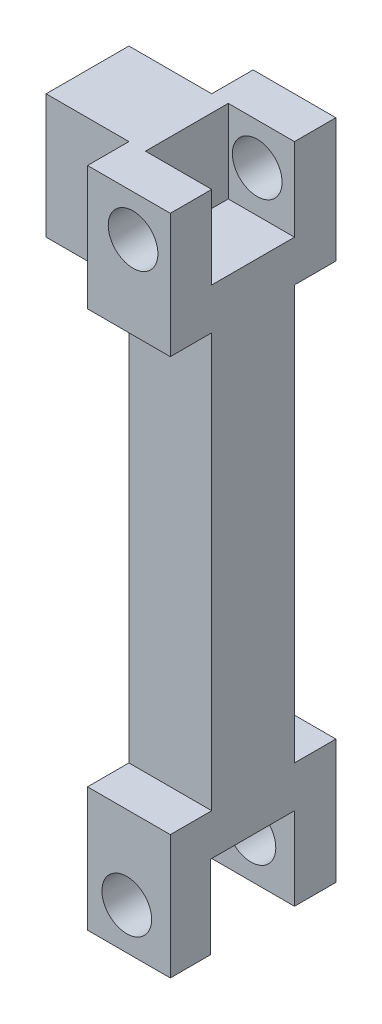
SolidWorks part; units mm, degrees
ref_plane "Front" through (0, 0, 0) normal (0, 0, 1) x (1, 0, 0)
ref_plane "Top" through (0, 0, 0) normal (0, 1, 0) x (1, 0, 0)
ref_plane "Right" through (0, 0, 0) normal (1, 0, 0) x (0, 0, -1)
sketch "Sketch1" plane through (0, 0, 0) normal (0, 0, 1) x (1, 0, 0)
  line L0 (-4.5761, -135.7066) -> (-29.9761, -135.7066)
  line L1 (-29.9761, 67.4934) -> (-4.5761, 67.4934)
  line L2 (-29.9761, 29.3934) -> (-29.9761, -135.7066)
  line L4 (-4.5761, 67.4934) -> (-4.5761, -135.7066)
  line L5 (-29.9761, 67.4934) -> (-55.3761, 67.4934)
  line L7 (-29.9761, 29.3934) -> (-55.3761, 29.3934)
  line L8 (-55.3761, 67.4934) -> (-55.3761, 29.3934)
  dimension "D1" = 25.4
  dimension "D2" = 203.2
  dimension "D3" = 25.4
  dimension "D4" = 38.1
extrude "Base-Extrude" add sketch "Sketch1" against normal blind 25.4
sketch "Sketch7" plane through (-29.9761, 0, 0) normal (-1, 0, 0) x (0, 0, 1)
  line L0 (0, 26.7505) -> (0, -135.7066) construction
  line L1 (-38.1, -135.7066) -> (-25.4, -135.7066)
  line L2 (-38.1, -135.7066) -> (-38.1, -97.6066)
  line L3 (-38.1, -97.6066) -> (-25.4, -97.6066)
  line L4 (12.7, -135.7066) -> (12.7, -97.6066)
  line L5 (-25.4, 26.7505) -> (-25.4, -135.7066) construction
  line L6 (0, -135.7066) -> (0, -97.6066)
  line L7 (-25.4, -135.7066) -> (-25.4, -97.6066)
  line L8 (0, -97.6066) -> (12.7, -97.6066)
  line L9 (0, -135.7066) -> (12.7, -135.7066)
  dimension "D1" = 12.7
  dimension "D2" = 12.7
  dimension "D3" = 38.1
extrude "Boss-Extrude5" add sketch "Sketch7" against normal blind 25.4
sketch "Sketch8" plane through (-29.9761, 0, 0) normal (-1, 0, 0) x (0, 0, 1)
  line L0 (-38.1, -135.7066) -> (12.7, -135.7066) construction
  line L1 (0.3517, -135.7066) -> (0.3517, -110.3066)
  line L2 (0.3517, -110.3066) -> (-25.4, -110.3066)
  line L3 (-25.4, -135.7066) -> (0.3517, -135.7066)
  line L4 (-25.4, -110.3066) -> (-25.4, -135.7066)
  dimension "D1" = 25.4
extrude "Cut-Extrude5" cut sketch "Sketch8" against normal up to vertex
sketch "Sketch11" plane through (-4.5761, 0, 0) normal (1, 0, 0) x (0, 0, -1)
  line L0 (25.4, 67.4934) -> (25.4, 29.3934)
  line L1 (-12.7, 67.4934) -> (0, 67.4934)
  line L2 (-12.7, 67.4934) -> (-12.7, 29.3934)
  line L3 (-12.7, 29.3934) -> (0, 29.3934)
  line L4 (38.1, 67.4934) -> (38.1, 29.3934)
  line L5 (0, 67.4934) -> (0, 29.3934)
  line L6 (25.4, 29.3934) -> (38.1, 29.3934)
  line L7 (25.4, 67.4934) -> (38.1, 67.4934)
  dimension "D1" = 12.7
  dimension "D2" = 12.7
  dimension "D3" = 38.1
extrude "Boss-Extrude6" add sketch "Sketch11" against normal up to vertex
sketch "Sketch12" plane through (-4.5761, 0, 0) normal (1, 0, 0) x (0, 0, -1)
  line L0 (38.1, 67.4934) -> (-12.7, 67.4934) construction
  line L1 (0, 67.4934) -> (25.4, 67.4934)
  line L2 (0, 67.4934) -> (0, 42.0934)
  line L3 (0, 42.0934) -> (25.4, 42.0934)
  line L4 (25.4, 67.4934) -> (25.4, 42.0934)
  dimension "D1" = 25.4
extrude "Cut-Extrude7" cut sketch "Sketch12" against normal blind 20.32
sketch "Sketch13" plane through (-55.3761, 0, 0) normal (-1, 0, 0) x (0, 0, 1)
  circle A0 centre (-13.0885, 49.4298) radius 7.62
extrude "Cut-Extrude8" cut sketch "Sketch13" against normal blind 20.32
sketch "Sketch14" plane through (0, 0, -38.1) normal (0, 0, -1) x (-1, 0, 0)
  line L1 (29.9761, 67.4934) -> (4.5761, 67.4934) construction
  line L2 (4.5761, -135.7066) -> (29.9761, -135.7066) construction
  line L3 (29.9761, 67.4934) -> (4.5761, 67.4934) construction
  line L4 (4.5761, -110.3066) -> (4.5761, -135.7066) construction
  circle A0 centre (16.0061, 54.7934) radius 7.62
  circle A1 centre (17.9313, -123.0066) radius 7.62
  point P14 (4.5761, -123.0066)
  dimension "D1" = 12.7
  dimension "D2" = 12.7
  dimension "D3" = 11.43
  dimension "D4" = 13.3552
extrude "Cut-Extrude9" cut sketch "Sketch14" against normal up to vertex
